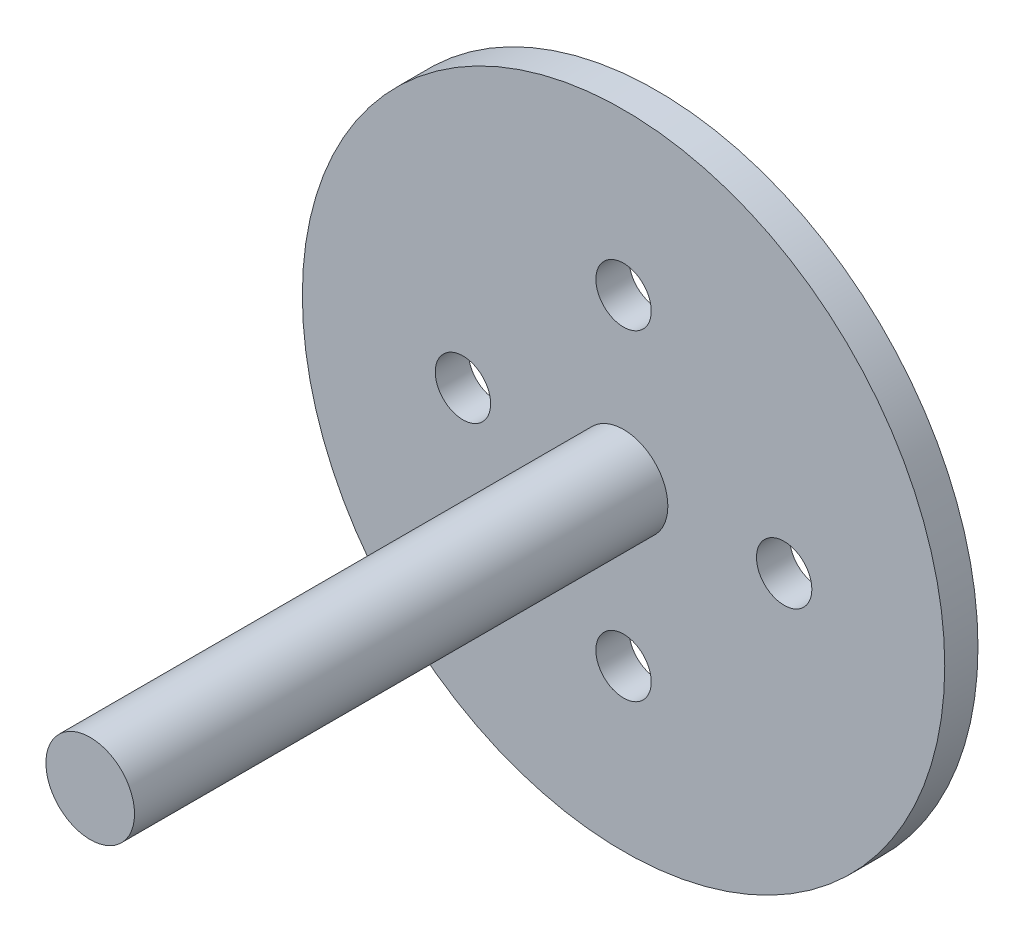
SolidWorks part; units mm, degrees
ref_plane "Front Plane" through (0, 0, 0) normal (0, 0, 1) x (1, 0, 0)
ref_plane "Top Plane" through (0, 0, 0) normal (0, 1, 0) x (1, 0, 0)
ref_plane "Right Plane" through (0, 0, 0) normal (1, 0, 0) x (0, 0, -1)
sketch "Sketch1" plane through (0, 0, 0) normal (0, 0, 1) x (1, 0, 0)
  circle A0 centre (0, 0) radius 29
  circle A5 centre (14.5, 0) radius 2.5
  circle A6 centre (-14.5, 0) radius 2.5
  circle A7 centre (0, 14.5) radius 2.5
  circle A8 centre (0, -14.5) radius 2.5
  dimension "D1" = 58
  dimension "D2" = 14.5
  dimension "D3" = 14.5
  dimension "D4" = 5
  dimension "D5" = 5
  dimension "D6" = 5
  dimension "D7" = 5
extrude "Plate" add sketch "Sketch1" along normal blind 3
sketch "Sketch2" plane through (0, 0, 3) normal (0, 0, 1) x (1, 0, 0)
  circle A0 centre (0, 0) radius 4
  dimension "D1" = 8
extrude "Middle_tube" add sketch "Sketch2" along normal blind 48.15
sketch "Sketch3" plane through (0, 0, 0) normal (0, 0, -1) x (-1, 0, 0)
  text T0 "UBC ROVER"
  point P1 (0, 0)
  point P4 (0, 0)
  point P5 (0, 0)
  point P6 (0, 0)
  point P7 (0, 0)
extrude "Boss-Extrude3" add sketch "Sketch3" along normal blind 2
